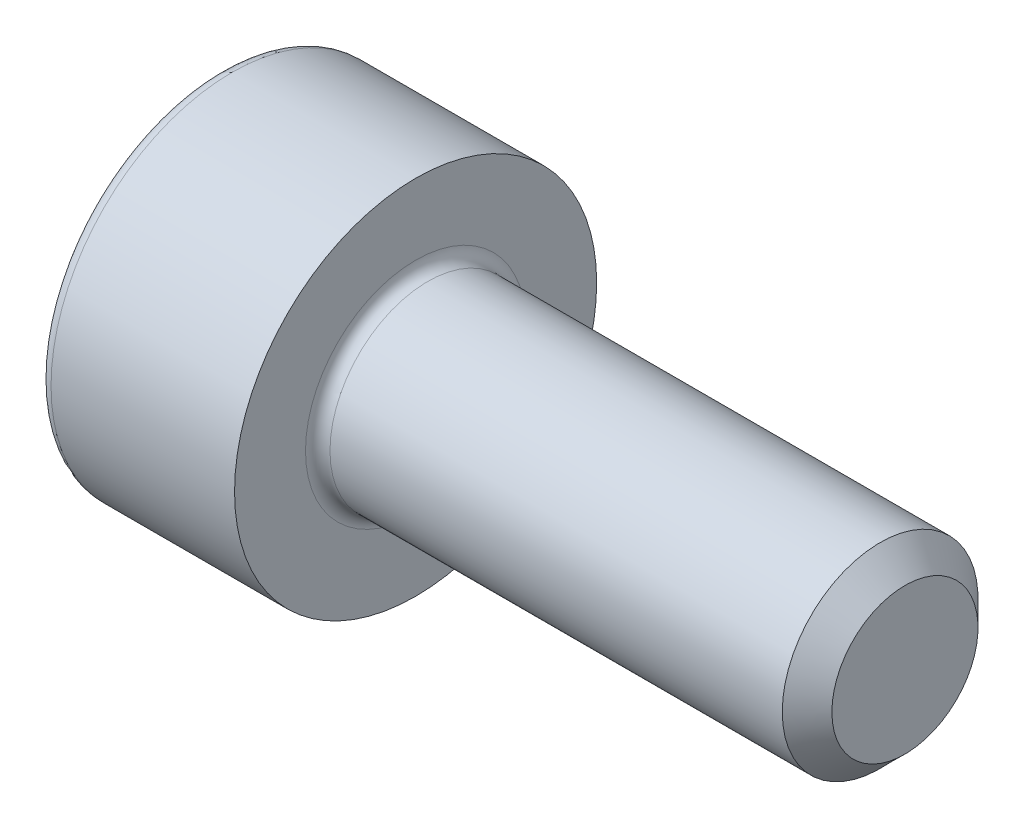
SolidWorks part; units mm, degrees
ref_plane "Front" through (0, 0, 0) normal (0, 0, 1) x (1, 0, 0)
ref_plane "Top" through (0, 0, 0) normal (0, 1, 0) x (1, 0, 0)
ref_plane "Right" through (0, 0, 0) normal (1, 0, 0) x (0, 0, -1)
sketch "Sketch1" plane through (0, 0, 0) normal (0, 0, 1) x (1, 0, 0)
  line L0 (4.7465, 1) -> (0.125, 1)
  line L1 (-2, 1.725) -> (-2, 0)
  line L2 (0, 1.85) -> (-1.875, 1.85)
  line L3 (0, 1.125) -> (0, 1.85)
  line L4 (5, 0.7465) -> (5, 0)
  line L5 (5, 0.7465) -> (4.7465, 1)
  line L6 (-2, 0) -> (0, 0) construction
  line L7 (-2, 0) -> (5, 0)
  arc A0 (-1.875, 1.85) -> (-2, 1.725) centre (-1.875, 1.725) ccw
  arc A1 (0, 1.125) -> (0.125, 1) centre (0.125, 1.125) ccw
  point P12 (0, 1.4875)
  dimension "D5" = 0.125
  dimension "D1" = 2
  dimension "D2" = 3.7
  dimension "D3" = 135
  dimension "D4" = 0.3585
  dimension "D6" = 5
  dimension "D7" = 2
revolve "Revolve1" add sketch "Sketch1" angle 360 about L7
sketch "Sketch2" plane through (-2, 0, 0) normal (-1, 0, 0) x (0, 0, 1)
  line L7 (0.75, 0.433) -> (0, 0.866)
  line L8 (0, 0.866) -> (-0.75, 0.433)
  line L9 (-0.75, 0.433) -> (-0.75, -0.433)
  line L10 (-0.75, -0.433) -> (0, -0.866)
  line L11 (0, -0.866) -> (0.75, -0.433)
  line L12 (0.75, -0.433) -> (0.75, 0.433)
  circle A0 centre (0, 0) radius 0.75 construction
  dimension "D1" = 1.5
extrude "Cut-Extrude1" cut sketch "Sketch2" against normal blind 1.1
